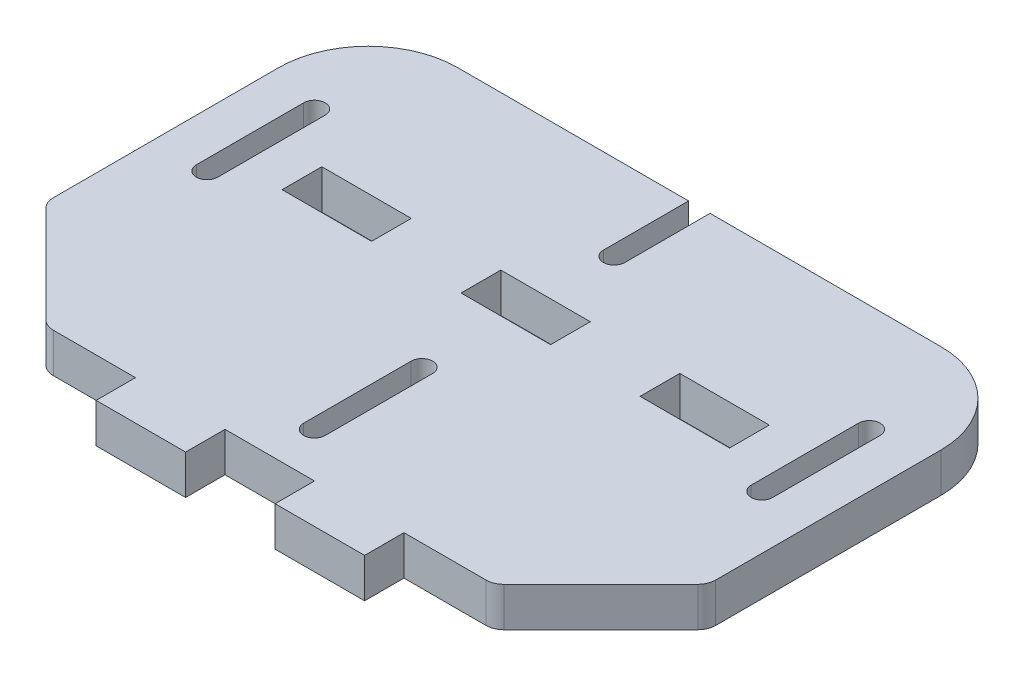
SolidWorks part; units mm, degrees
ref_plane "Front Plane" through (0, 0, 0) normal (0, 0, 1) x (1, 0, 0)
ref_plane "Top Plane" through (0, 0, 0) normal (0, 1, 0) x (1, 0, 0)
ref_plane "Right Plane" through (0, 0, 0) normal (1, 0, 0) x (0, 0, -1)
sketch "Sketch1" plane through (0, 0, 0) normal (0, 1, 0) x (1, 0, 0)
  line L8 (0, -7.5) -> (125, -7.5)
  line L12 (0, -7.5) -> (0, 3.5)
  line L14 (125, -7.5) -> (125, 3.5)
  line L17 (155, 33.5) -> (155, 123.5)
  line L18 (-30, 33.5) -> (-30, 123.5)
  line L23 (140, 63.5) -> (140, 93.5) construction
  line L24 (137, 63.5) -> (137, 93.5)
  line L25 (143, 63.5) -> (143, 93.5)
  line L26 (-15, 63.5) -> (-15, 93.5) construction
  line L27 (-18, 63.5) -> (-18, 93.5)
  line L28 (-12, 63.5) -> (-12, 93.5)
  line L29 (62.5, 16) -> (62.5, 46) construction
  line L30 (59.5, 16) -> (59.5, 46)
  line L31 (65.5, 16) -> (65.5, 46)
  line L32 (59.5, 123.5) -> (-30, 123.5)
  line L33 (65.5, 123.5) -> (65.5, 99.7057)
  line L34 (59.5, 123.5) -> (59.5, 99.7057)
  line L35 (155, 123.5) -> (65.5, 123.5)
  line L36 (125, 3.5) -> (155, 33.5)
  line L37 (0, 3.5) -> (-30, 33.5)
  arc A0 (137, 63.5) -> (143, 63.5) centre (140, 63.5) ccw
  arc A1 (143, 93.5) -> (137, 93.5) centre (140, 93.5) ccw
  arc A2 (-18, 63.5) -> (-12, 63.5) centre (-15, 63.5) ccw
  arc A3 (-12, 93.5) -> (-18, 93.5) centre (-15, 93.5) ccw
  arc A4 (59.5, 16) -> (65.5, 16) centre (62.5, 16) ccw
  arc A5 (65.5, 46) -> (59.5, 46) centre (62.5, 46) ccw
  arc A7 (59.5, 99.7057) -> (65.5, 99.7057) centre (62.5, 99.7057) ccw
  point P4 (-30, 78.5)
  point P18 (140, 78.5)
  point P23 (-15, 78.5)
  point P30 (62.5, 31)
  dimension "D7" = 15
  dimension "D8" = 45
  dimension "D10" = 30
  dimension "D13" = 15
  dimension "D1" = 89.5
  dimension "D12" = 3
  dimension "D2" = 135
  dimension "D3" = 11
  dimension "D4" = 135
  dimension "D5" = 125
  dimension "D6" = 90
extrude "Boss-Extrude6" add sketch "Sketch1" along normal blind 11
sketch "Sketch4" plane through (0, 11, 0) normal (0, 1, 0) x (1, 0, 0)
  line L0 (0, -7.5) -> (125, -7.5) construction
  line L1 (0, -7.5) -> (25, -7.5)
  line L2 (0, -7.5) -> (0, 3.5)
  line L3 (0, 3.5) -> (25, 3.5)
  line L4 (25, -7.5) -> (25, 3.5)
  line L5 (50, -7.5) -> (75, -7.5)
  line L6 (50, -7.5) -> (50, 3.5)
  line L7 (50, 3.5) -> (75, 3.5)
  line L8 (75, -7.5) -> (75, 3.5)
  line L9 (0, 69.45) -> (25, 69.45)
  line L10 (125, -7.5) -> (100, -7.5)
  line L11 (125, -7.5) -> (125, 3.5)
  line L12 (125, 3.5) -> (100, 3.5)
  line L13 (100, -7.5) -> (100, 3.5)
  line L14 (0, 69.45) -> (0, 80.55)
  line L15 (0, 80.55) -> (25, 80.55)
  line L16 (25, 69.45) -> (25, 80.55)
  line L17 (50, 69.45) -> (75, 69.45)
  line L18 (50, 69.45) -> (50, 80.55)
  line L19 (50, 80.55) -> (75, 80.55)
  line L20 (75, 69.45) -> (75, 80.55)
  line L21 (125, 69.45) -> (100, 69.45)
  line L22 (125, 69.45) -> (125, 80.55)
  line L23 (125, 80.55) -> (100, 80.55)
  line L24 (100, 69.45) -> (100, 80.55)
  point P30 (125, 75)
  dimension "D1" = 25
  dimension "D2" = 25
  dimension "D3" = 25
  dimension "D4" = 25
  dimension "D5" = 82.5
  dimension "D6" = 11.1
extrude "Cut-Extrude1" cut sketch "Sketch4" against normal through all
fillet "Fillet1" radius 25 2 edges at (155, 5.5, -123.5) (-30, 5.5, -123.5)
fillet "Fillet2" radius 5 4 edges at (155, 5.5, -33.5) (125, 5.5, -3.5) (0, 5.5, -3.5) (-30, 5.5, -33.5)
